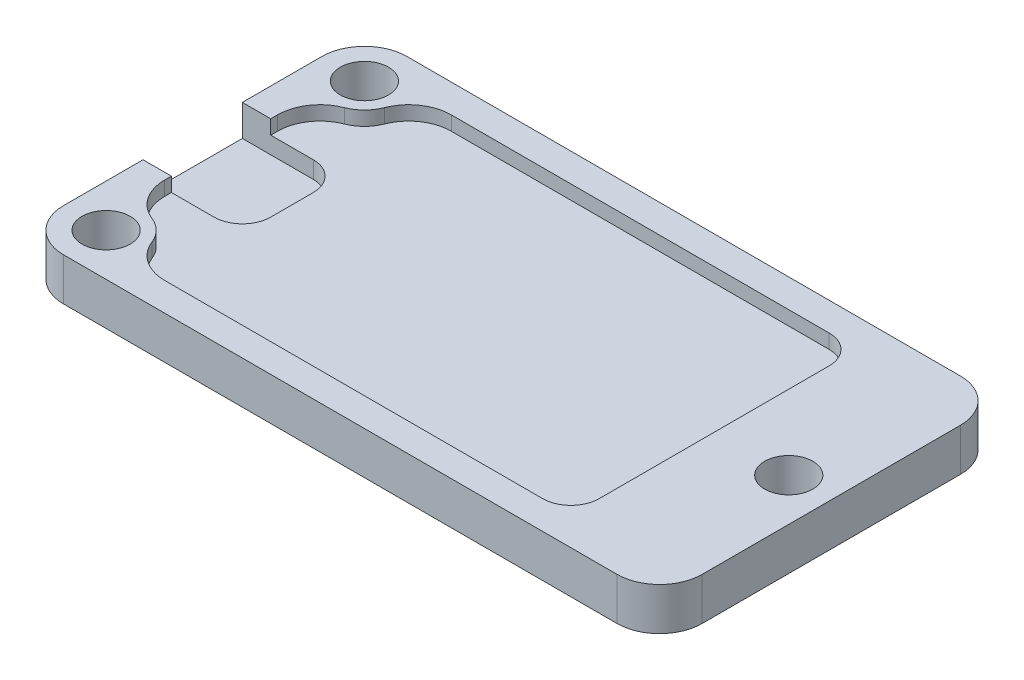
SolidWorks part; units mm, degrees
material "3.1355 (EN-AW 2024)"
ref_plane "Спереди" through (0, 0, 0) normal (0, 0, 1) x (1, 0, 0)
ref_plane "Сверху" through (0, 0, 0) normal (0, 1, 0) x (1, 0, 0)
ref_plane "Справа" through (0, 0, 0) normal (1, 0, 0) x (0, 0, -1)
sketch "Эскиз1" plane through (0, 0, 0) normal (0, 1, 0) x (1, 0, 0)
  line L1 (0, 0) -> (45, 0)
  line L2 (0, 0) -> (0, 24.2)
  line L3 (0, 24.2) -> (45, 24.2)
  line L4 (45, 0) -> (45, 24.2)
  dimension "D1" = 24.2
  dimension "D2" = 45
extrude "Бобышка-Вытянуть1" add sketch "Эскиз1" along normal blind 3
fillet "Скругление1" radius 3 4 edges at (0, 1.5, 0) (45, 1.5, 0) (45, 1.5, -24.2) (0, 1.5, -24.2)
sketch "Эскиз4" plane through (0, 3, 0) normal (0, 1, 0) x (1, 0, 0)
  line L1 (3, 3) -> (42, 3)
  line L2 (3, 3) -> (3, 21.2)
  line L3 (3, 21.2) -> (42, 21.2)
  line L4 (42, 3) -> (42, 21.2)
  point P4 (3, 21.2)
  point P5 (42, 3)
hole_wizard "Отверстие с зазором M31" positions "Эскиз5" profile "Эскиз6" hole size "M3" standard "Ansi Metric"
sketch "Эскиз5" plane through (69.4238, 0, -24.0901) normal (0, -1, 0) x (0, 0, 1)
  point P0 (2.8901, 66.4238)
  point P3 (21.0901, 66.4238)
  point P6 (11.9901, 27.4238)
sketch "Эскиз6" plane through (3, 0, -21.2) normal (1, 0, 0) x (0, 0, -1)
  line L0 (0, 0) -> (0, 4.0215)
  line L1 (0, 4.0215) -> (1.7, 3)
  line L2 (1.7, 3) -> (1.7, 0)
  line L3 (1.7, 0) -> (0, 0)
  line L4 (0, 4.0215) -> (-1.7, 3) construction
  line L5 (0, -6.35) -> (0, 107.95) construction
  dimension "Диаметр отверстия" = 3.4
  dimension "Глубина отверстия" = 3
  dimension "Угол заточки сверла" = 118
sketch "Эскиз7" plane through (0, 3, 0) normal (0, 1, 0) x (1, 0, 0)
  line L1 (2, 8.1235) -> (2, 16.0765) construction
  line L2 (8.1235, 22.2) -> (36.7526, 22.2) construction
  line L3 (36.7526, 2) -> (8.1235, 2) construction
  line L4 (2, 8.1235) -> (2, 16.0765)
  line L5 (8.1235, 22.2) -> (36.7526, 22.2)
  line L6 (36.7526, 2) -> (8.1235, 2)
  line L7 (36.7526, 2) -> (36.7526, 22.2)
  arc A1 (5.3289, 3.9091) -> (8.1235, 2) centre (8.1235, 5) ccw construction
  arc A2 (5.3289, 3.9091) -> (3.9091, 5.3289) centre (3, 3) ccw construction
  arc A3 (2, 8.1235) -> (3.9091, 5.3289) centre (5, 8.1235) ccw construction
  arc A4 (3.9091, 18.8711) -> (2, 16.0765) centre (5, 16.0765) ccw construction
  arc A5 (3.9091, 18.8711) -> (5.3289, 20.2909) centre (3, 21.2) ccw construction
  arc A6 (8.1235, 22.2) -> (5.3289, 20.2909) centre (8.1235, 19.2) ccw construction
  arc A7 (5.3289, 3.9091) -> (8.1235, 2) centre (8.1235, 5) ccw
  arc A8 (5.3289, 3.9091) -> (3.9091, 5.3289) centre (3, 3) ccw
  arc A9 (2, 8.1235) -> (3.9091, 5.3289) centre (5, 8.1235) ccw
  arc A10 (3.9091, 18.8711) -> (2, 16.0765) centre (5, 16.0765) ccw
  arc A11 (3.9091, 18.8711) -> (5.3289, 20.2909) centre (3, 21.2) ccw
  arc A12 (8.1235, 22.2) -> (5.3289, 20.2909) centre (8.1235, 19.2) ccw
extrude "Вырез-Вытянуть1" cut sketch "Эскиз7" against normal blind 1
fillet "Скругление2" radius 2 2 edges at (36.7526, 2.5, -2) (36.7526, 2.5, -22.2)
sketch "Эскиз3" plane through (0, 3, 0) normal (0, 1, 0) x (1, 0, 0)
  line L0 (0, 8.6) -> (0, 15.6)
  line L1 (0, 21.2) -> (0, 3) construction
  line L2 (0, 15.6) -> (7, 15.6)
  line L4 (7, 8.6) -> (0, 8.6)
  line L6 (7, 15.6) -> (7, 8.6)
  point P4 (0, 12.1)
  dimension "D1" = 7
  dimension "D2" = 7
extrude "Вырез-Вытянуть2" cut sketch "Эскиз3" against normal blind 2.2
fillet "Скругление3" radius 2 2 edges at (7, 1.4, -8.6) (7, 1.4, -15.6)
